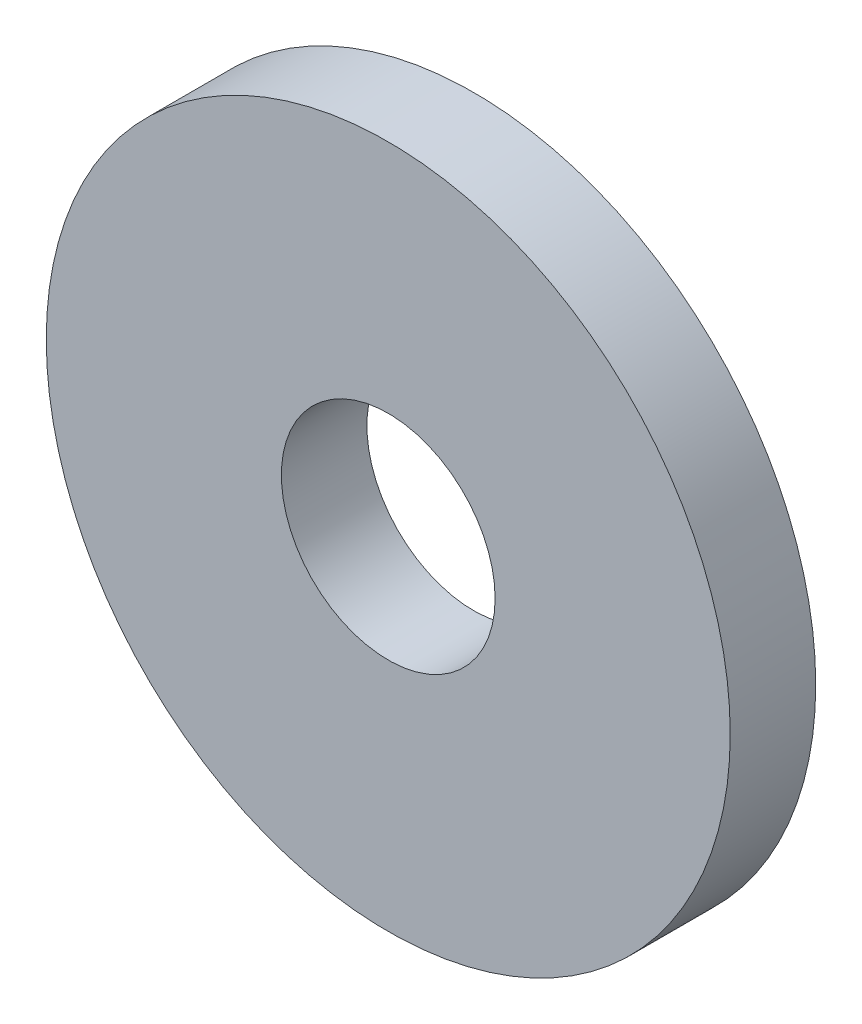
SolidWorks part; units mm, degrees
ref_plane "Front Plane" through (0, 0, 0) normal (0, 0, 1) x (1, 0, 0)
ref_plane "Top Plane" through (0, 0, 0) normal (0, 1, 0) x (1, 0, 0)
ref_plane "Right Plane" through (0, 0, 0) normal (1, 0, 0) x (0, 0, -1)
sketch "Sketch1" plane through (0, 0, 0) normal (0, 0, 1) x (1, 0, 0)
  circle A0 centre (0, 0) radius 8
  circle A1 centre (0, 0) radius 2.5
  dimension "D1" = 16
  dimension "D2" = 5
extrude "Boss-Extrude1" add sketch "Sketch1" along normal blind 2
